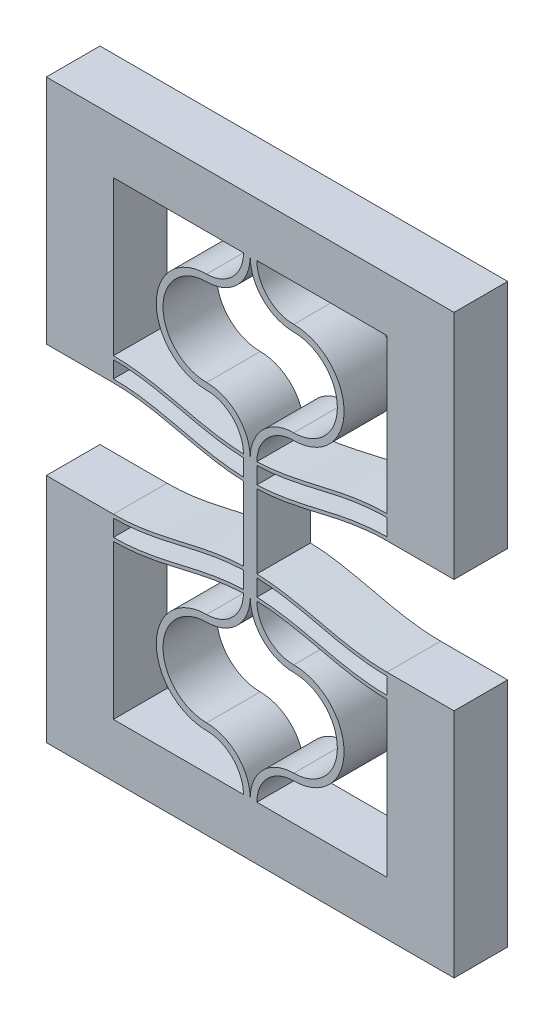
SolidWorks part; units mm, degrees
ref_plane "Front Plane" through (0, 0, 0) normal (0, 0, 1) x (1, 0, 0)
ref_plane "Top Plane" through (0, 0, 0) normal (0, 1, 0) x (1, 0, 0)
ref_plane "Right Plane" through (0, 0, 0) normal (1, 0, 0) x (0, 0, -1)
sketch "Sketch1" plane through (0, 0, 0) normal (0, 0, 1) x (1, 0, 0)
  line L4 (0, 11.5) -> (0, 0)
  line L5 (10.2, 0) -> (10.2, 13) construction
  line L6 (10.2, 13) -> (10.2, 15.9911) construction
  line L17 (9.7, 0) -> (0, 0)
  line L18 (10.7, 0) -> (20.4, 0)
  line L19 (20.4, 0) -> (20.4, 11.5)
  line L20 (10.7, 13.2411) -> (10.7, 14.4911)
  line L21 (9.7, 13.2411) -> (9.7, 14.4911)
  line L22 (10.7, 14.7411) -> (10.7, 15.9911)
  line L23 (10.7, 15.9911) -> (9.7, 15.9911)
  line L24 (9.7, 15.9911) -> (9.7, 14.7411)
  line L31 (-5, 13.25) -> (-5, -4)
  line L32 (-5, -4) -> (25.4, -4)
  line L33 (25.4, -4) -> (25.4, 13.25)
  line L34 (0, 11.75) -> (0, 13)
  line L36 (-5, 13.25) -> (0, 13.25)
  line L37 (25.4, 13.25) -> (20.4, 13.25)
  line L38 (20.4, 11.75) -> (20.4, 13)
  arc A0 (10.2, 13) -> (6.95, 9.75) centre (6.95, 13) cw
  arc A1 (6.95, 9.75) -> (6.95, 3.25) centre (6.95, 6.5) ccw
  arc A2 (6.95, 3.25) -> (10.2, 0) centre (6.95, 0) cw
  arc A3 (9.7, 12.9911) -> (6.95, 10.25) centre (6.95, 13) cw
  arc A4 (6.95, 10.25) -> (6.95, 2.75) centre (6.95, 6.5) ccw
  arc A5 (6.95, 2.75) -> (9.7, 0) centre (6.95, 0) cw
  arc A6 (9.7, 13) -> (6.95, 10.25) centre (6.95, 13) cw construction
  arc A7 (13.45, 3.25) -> (10.2, 0) centre (13.45, 0) ccw
  arc A8 (13.45, 2.75) -> (10.7, 0) centre (13.45, 0) ccw
  arc A9 (13.45, 9.75) -> (13.45, 3.25) centre (13.45, 6.5) cw
  arc A10 (13.45, 10.25) -> (13.45, 2.75) centre (13.45, 6.5) cw
  arc A11 (10.7, 12.9911) -> (13.45, 10.25) centre (13.45, 13) ccw
  arc A12 (10.2, 13) -> (13.45, 9.75) centre (13.45, 13) ccw
  spline S0 degree 4 poles (-2.0401, 11.8932) (-1.9772, 11.8846) (-1.8455, 11.8679) (-1.6624, 11.8447) (-1.3945, 11.8179) (-1.0936, 11.7897) (-0.7437, 11.7688) (-0.4752, 11.7554) (-0.0408, 11.749) (0.1102, 11.7499) (0.4738, 11.7558) (0.7092, 11.7679) (1.0334, 11.7851) (1.3516, 11.8128) (1.7502, 11.854) (2.1923, 11.9124) (2.7058, 11.9922) (3.3058, 12.1029) (4.0022, 12.2485) (4.9166, 12.4561) (5.9838, 12.707) (7.055, 12.9379) (8.1373, 13.1142) (9.0337, 13.2105) (9.8109, 13.2536) (10.5891, 13.2536) (11.3663, 13.2105) (12.2627, 13.1142) (13.3449, 12.9379) (14.4163, 12.707) (15.4832, 12.4561) (16.3198, 12.2662) (16.8578, 12.1523) (17.3629, 12.0533) (17.7764, 11.9798) (18.2035, 11.9124) (18.6563, 11.854) (18.9878, 11.8179) (19.2899, 11.793) (19.5137, 11.7765) (19.7423, 11.7659) (19.9174, 11.7558) (20.2941, 11.7499) (20.4363, 11.749) (20.8074, 11.7542) (21.0192, 11.7634) (21.2671, 11.7754) (21.4449, 11.7884) (21.6432, 11.8037) (21.8311, 11.8212) (22.0262, 11.8414) (22.2161, 11.864) (22.3445, 11.8804) (22.4082, 11.8889) (22.4399, 11.8932) knots 0 0 0 0 0 0.010394 0.020788 0.031182 0.041576 0.062112 0.07238 0.082649 0.098356 0.106209 0.114063 0.12977 0.145477 0.161184 0.176891 0.202819 0.228747 0.260161 0.291575 0.354403 0.405758 0.437172 0.468586 0.5 0.531414 0.562828 0.594242 0.645597 0.708425 0.739839 0.771253 0.784217 0.797181 0.823109 0.838816 0.854523 0.87023 0.878084 0.885937 0.893791 0.901644 0.917351 0.92762 0.937888 0.948156 0.958424 0.963621 0.968818 0.979212 0.989606 0.994803 1 1 1 1 1 construction
  spline S1 degree 4 poles (0, 11.75) (0.0812, 11.75) (0.1997, 11.7513) (0.4738, 11.7558) (0.7092, 11.7679) (1.0334, 11.7851) (1.3516, 11.8128) (1.7502, 11.854) (2.1923, 11.9124) (2.7058, 11.9922) (3.3058, 12.1029) (4.0022, 12.2485) (4.9166, 12.4561) (5.9838, 12.707) (7.055, 12.9379) (8.1373, 13.1142) (9.0337, 13.2105) (9.8109, 13.2536) (10.5891, 13.2536) (11.3663, 13.2105) (12.2627, 13.1142) (13.3449, 12.9379) (14.4163, 12.707) (15.4832, 12.4561) (16.3198, 12.2662) (16.8578, 12.1523) (17.3629, 12.0533) (17.7764, 11.9798) (18.2035, 11.9124) (18.6563, 11.854) (18.9878, 11.8179) (19.2899, 11.793) (19.5137, 11.7765) (19.7423, 11.7659) (19.9174, 11.7558) (20.2013, 11.7513) (20.3188, 11.75) (20.4, 11.75) knots 0.082649 0.082649 0.082649 0.082649 0.082649 0.098356 0.106209 0.114063 0.12977 0.145477 0.161184 0.176891 0.202819 0.228747 0.260161 0.291575 0.354403 0.405758 0.437172 0.468586 0.5 0.531414 0.562828 0.594242 0.645597 0.708425 0.739839 0.771253 0.784217 0.797181 0.823109 0.838816 0.854523 0.87023 0.878084 0.885937 0.893791 0.901644 0.917351 0.917351 0.917351 0.917351 0.917351
  spline S2 degree 4 poles (-2.0401, 13.1432) (-1.9772, 13.1346) (-1.8455, 13.1179) (-1.6624, 13.0947) (-1.3945, 13.0679) (-1.0936, 13.0397) (-0.7437, 13.0188) (-0.4752, 13.0054) (-0.0408, 12.999) (0.1102, 12.9999) (0.4738, 13.0058) (0.7092, 13.0179) (1.0334, 13.0351) (1.3516, 13.0628) (1.7502, 13.104) (2.1923, 13.1624) (2.7058, 13.2422) (3.3058, 13.3529) (4.0022, 13.4985) (4.9166, 13.7061) (5.9838, 13.957) (7.055, 14.1879) (8.1373, 14.3642) (9.0337, 14.4605) (9.8109, 14.5036) (10.5891, 14.5036) (11.3663, 14.4605) (12.2627, 14.3642) (13.3449, 14.1879) (14.4163, 13.957) (15.4832, 13.7061) (16.3198, 13.5162) (16.8578, 13.4023) (17.3629, 13.3033) (17.7764, 13.2298) (18.2035, 13.1624) (18.6563, 13.104) (18.9878, 13.0679) (19.2899, 13.043) (19.5137, 13.0265) (19.7423, 13.0159) (19.9174, 13.0058) (20.2941, 12.9999) (20.4363, 12.999) (20.8074, 13.0042) (21.0192, 13.0134) (21.2671, 13.0254) (21.4449, 13.0384) (21.6432, 13.0537) (21.8311, 13.0712) (22.0262, 13.0914) (22.2161, 13.114) (22.3445, 13.1304) (22.4082, 13.1389) (22.4399, 13.1432) knots 0 0 0 0 0 0.010394 0.020788 0.031182 0.041576 0.062112 0.07238 0.082649 0.098356 0.106209 0.114063 0.12977 0.145477 0.161184 0.176891 0.202819 0.228747 0.260161 0.291575 0.354403 0.405758 0.437172 0.468586 0.5 0.531414 0.562828 0.594242 0.645597 0.708425 0.739839 0.771253 0.784217 0.797181 0.823109 0.838816 0.854523 0.87023 0.878084 0.885937 0.893791 0.901644 0.917351 0.92762 0.937888 0.948156 0.958424 0.963621 0.968818 0.979212 0.989606 0.994803 1 1 1 1 1 construction
  spline S3 degree 4 poles (0, 13) (0.0812, 13) (0.1997, 13.0013) (0.4738, 13.0058) (0.7092, 13.0179) (1.0334, 13.0351) (1.3516, 13.0628) (1.7502, 13.104) (2.1923, 13.1624) (2.7058, 13.2422) (3.3058, 13.3529) (4.0022, 13.4985) (4.9166, 13.7061) (5.9838, 13.957) (7.055, 14.1879) (8.1373, 14.3642) (9.0337, 14.4605) (9.8109, 14.5036) (10.5891, 14.5036) (11.3663, 14.4605) (12.2627, 14.3642) (13.3449, 14.1879) (14.4163, 13.957) (15.4832, 13.7061) (16.3198, 13.5162) (16.8578, 13.4023) (17.3629, 13.3033) (17.7764, 13.2298) (18.2035, 13.1624) (18.6563, 13.104) (18.9878, 13.0679) (19.2899, 13.043) (19.5137, 13.0265) (19.7423, 13.0159) (19.9174, 13.0058) (20.2013, 13.0013) (20.3188, 13) (20.4, 13) knots 0.082649 0.082649 0.082649 0.082649 0.082649 0.098356 0.106209 0.114063 0.12977 0.145477 0.161184 0.176891 0.202819 0.228747 0.260161 0.291575 0.354403 0.405758 0.437172 0.468586 0.5 0.531414 0.562828 0.594242 0.645597 0.708425 0.739839 0.771253 0.784217 0.797181 0.823109 0.838816 0.854523 0.87023 0.878084 0.885937 0.893791 0.901644 0.917351 0.917351 0.917351 0.917351 0.917351
  spline S4 degree 4 poles (-2.0401, 13.3932) (-1.9772, 13.3846) (-1.8455, 13.3679) (-1.6624, 13.3447) (-1.3945, 13.3179) (-1.0936, 13.2897) (-0.7437, 13.2688) (-0.4752, 13.2554) (-0.0408, 13.249) (0.1102, 13.2499) (0.4738, 13.2558) (0.7092, 13.2679) (1.0334, 13.2851) (1.3516, 13.3128) (1.7502, 13.354) (2.1923, 13.4124) (2.7058, 13.4922) (3.3058, 13.6029) (4.0022, 13.7485) (4.9166, 13.9561) (5.9838, 14.207) (7.055, 14.4379) (8.1373, 14.6142) (9.0337, 14.7105) (9.8109, 14.7536) (10.5891, 14.7536) (11.3663, 14.7105) (12.2627, 14.6142) (13.3449, 14.4379) (14.4163, 14.207) (15.4832, 13.9561) (16.3198, 13.7662) (16.8578, 13.6523) (17.3629, 13.5533) (17.7764, 13.4798) (18.2035, 13.4124) (18.6563, 13.354) (18.9878, 13.3179) (19.2899, 13.293) (19.5137, 13.2765) (19.7423, 13.2659) (19.9174, 13.2558) (20.2941, 13.2499) (20.4363, 13.249) (20.8074, 13.2542) (21.0192, 13.2634) (21.2671, 13.2754) (21.4449, 13.2884) (21.6432, 13.3037) (21.8311, 13.3212) (22.0262, 13.3414) (22.2161, 13.364) (22.3445, 13.3804) (22.4082, 13.3889) (22.4399, 13.3932) knots 0 0 0 0 0 0.010394 0.020788 0.031182 0.041576 0.062112 0.07238 0.082649 0.098356 0.106209 0.114063 0.12977 0.145477 0.161184 0.176891 0.202819 0.228747 0.260161 0.291575 0.354403 0.405758 0.437172 0.468586 0.5 0.531414 0.562828 0.594242 0.645597 0.708425 0.739839 0.771253 0.784217 0.797181 0.823109 0.838816 0.854523 0.87023 0.878084 0.885937 0.893791 0.901644 0.917351 0.92762 0.937888 0.948156 0.958424 0.963621 0.968818 0.979212 0.989606 0.994803 1 1 1 1 1 construction
  spline S5 degree 4 poles (0, 13.25) (0.0812, 13.25) (0.1997, 13.2513) (0.4738, 13.2558) (0.7092, 13.2679) (1.0334, 13.2851) (1.3516, 13.3128) (1.7502, 13.354) (2.1923, 13.4124) (2.7058, 13.4922) (3.3058, 13.6029) (4.0022, 13.7485) (4.9166, 13.9561) (5.9838, 14.207) (7.055, 14.4379) (8.1373, 14.6142) (9.0337, 14.7105) (9.8109, 14.7536) (10.5891, 14.7536) (11.3663, 14.7105) (12.2627, 14.6142) (13.3449, 14.4379) (14.4163, 14.207) (15.4832, 13.9561) (16.3198, 13.7662) (16.8578, 13.6523) (17.3629, 13.5533) (17.7764, 13.4798) (18.2035, 13.4124) (18.6563, 13.354) (18.9878, 13.3179) (19.2899, 13.293) (19.5137, 13.2765) (19.7423, 13.2659) (19.9174, 13.2558) (20.2013, 13.2513) (20.3188, 13.25) (20.4, 13.25) knots 0.082649 0.082649 0.082649 0.082649 0.082649 0.098356 0.106209 0.114063 0.12977 0.145477 0.161184 0.176891 0.202819 0.228747 0.260161 0.291575 0.354403 0.405758 0.437172 0.468586 0.5 0.531414 0.562828 0.594242 0.645597 0.708425 0.739839 0.771253 0.784217 0.797181 0.823109 0.838816 0.854523 0.87023 0.878084 0.885937 0.893791 0.901644 0.917351 0.917351 0.917351 0.917351 0.917351
  spline S8 degree 4 poles (-2.0401, 11.6432) (-1.9772, 11.6346) (-1.8455, 11.6179) (-1.6624, 11.5947) (-1.3945, 11.5679) (-1.0936, 11.5397) (-0.7437, 11.5188) (-0.4752, 11.5054) (-0.0408, 11.499) (0.1102, 11.4999) (0.4738, 11.5058) (0.7092, 11.5179) (1.0334, 11.5351) (1.3516, 11.5628) (1.7502, 11.604) (2.1923, 11.6624) (2.7058, 11.7422) (3.3058, 11.8529) (4.0022, 11.9985) (4.9166, 12.2061) (5.9838, 12.457) (7.055, 12.6879) (8.1373, 12.8642) (9.0337, 12.9605) (9.8109, 13.0036) (10.5891, 13.0036) (11.3663, 12.9605) (12.2627, 12.8642) (13.3449, 12.6879) (14.4163, 12.457) (15.4832, 12.2061) (16.3198, 12.0162) (16.8578, 11.9023) (17.3629, 11.8033) (17.7764, 11.7298) (18.2035, 11.6624) (18.6563, 11.604) (18.9878, 11.5679) (19.2899, 11.543) (19.5137, 11.5265) (19.7423, 11.5159) (19.9174, 11.5058) (20.2941, 11.4999) (20.4363, 11.499) (20.8074, 11.5042) (21.0192, 11.5134) (21.2671, 11.5254) (21.4449, 11.5384) (21.6432, 11.5537) (21.8311, 11.5712) (22.0262, 11.5914) (22.2161, 11.614) (22.3445, 11.6304) (22.4082, 11.6389) (22.4399, 11.6432) knots 0 0 0 0 0 0.010394 0.020788 0.031182 0.041576 0.062112 0.07238 0.082649 0.098356 0.106209 0.114063 0.12977 0.145477 0.161184 0.176891 0.202819 0.228747 0.260161 0.291575 0.354403 0.405758 0.437172 0.468586 0.5 0.531414 0.562828 0.594242 0.645597 0.708425 0.739839 0.771253 0.784217 0.797181 0.823109 0.838816 0.854523 0.87023 0.878084 0.885937 0.893791 0.901644 0.917351 0.92762 0.937888 0.948156 0.958424 0.963621 0.968818 0.979212 0.989606 0.994803 1 1 1 1 1 construction
  spline S9 degree 4 poles (0, 11.5) (0.0812, 11.5) (0.1997, 11.5013) (0.4738, 11.5058) (0.7092, 11.5179) (1.0334, 11.5351) (1.3516, 11.5628) (1.7502, 11.604) (2.1923, 11.6624) (2.7058, 11.7422) (3.3058, 11.8529) (4.0022, 11.9985) (4.9166, 12.2061) (5.9838, 12.457) (7.055, 12.6879) (8.1373, 12.8642) (9.0337, 12.9605) (9.8109, 13.0036) (10.5891, 13.0036) (11.3663, 12.9605) (12.2627, 12.8642) (13.3449, 12.6879) (14.4163, 12.457) (15.4832, 12.2061) (16.3198, 12.0162) (16.8578, 11.9023) (17.3629, 11.8033) (17.7764, 11.7298) (18.2035, 11.6624) (18.6563, 11.604) (18.9878, 11.5679) (19.2899, 11.543) (19.5137, 11.5265) (19.7423, 11.5159) (19.9174, 11.5058) (20.2013, 11.5013) (20.3188, 11.5) (20.4, 11.5) knots 0.082649 0.082649 0.082649 0.082649 0.082649 0.098356 0.106209 0.114063 0.12977 0.145477 0.161184 0.176891 0.202819 0.228747 0.260161 0.291575 0.354403 0.405758 0.437172 0.468586 0.5 0.531414 0.562828 0.594242 0.645597 0.708425 0.739839 0.771253 0.784217 0.797181 0.823109 0.838816 0.854523 0.87023 0.878084 0.885937 0.893791 0.901644 0.917351 0.917351 0.917351 0.917351 0.917351
  dimension "D4" = 0.25
  dimension "D6" = 4
  dimension "D1" = 13
  dimension "D2" = 0.5
  dimension "D3" = 0.25
  dimension "D7" = 5
  dimension "D5" = 1.5
extrude "Boss-Extrude1" add sketch "Sketch1" along normal blind 4
sketch "Sketch4" plane through (0, 15.9911, 0) normal (0, 1, 0) x (1, 0, 0)
  line L24 (10.7, 0) -> (9.7, 0)
  line L25 (9.7, 0) -> (9.7, -4)
  line L26 (10.7, 0) -> (9.7, 0)
  line L27 (10.7, -4) -> (10.7, 0)
  line L29 (9.7, 0) -> (9.7, -4)
  line L31 (10.7, -4) -> (10.7, 0)
  line L32 (9.7, -4) -> (10.7, -4)
  line L33 (9.7, -4) -> (10.7, -4)
  dimension "D1" = 0
extrude "Boss-Extrude2" add sketch "Sketch4" along normal blind 1.5
mirror "Mirror3" about plane through (0, 17.4911, 0) normal (0, 1, 0) of bodies 179
ref_plane "Plane1" through (10.2, 0, 0) normal (-1, 0, 0) x (0, 0, 1)
split "Split2" [suppressed] bodies to split 247 102
sketch "Sketch7" [suppressed] plane through (10.2, 0, 0) normal (-1, 0, 0) x (0, 0, 1)
  line L4 (4, 34.9822) -> (4, 38.9822)
  line L12 (0, 13) -> (4, 13)
  line L13 (0, 13) -> (4, 13)
  line L14 (4, 13) -> (4, 21.9822)
  line L15 (4, 13) -> (4, 21.9822)
  line L20 (4, 0) -> (0, 0)
  line L22 (4, 0) -> (0, 0)
  line L23 (0, -4) -> (4, -4)
  line L27 (0, -4) -> (4, -4)
  line L31 (4, 21.9822) -> (0, 21.9822)
  line L32 (4, 21.9822) -> (0, 21.9822)
  line L33 (0, 21.9822) -> (0, 13)
  line L34 (0, 21.9822) -> (0, 13)
  line L36 (4, -4) -> (4, 0)
  line L38 (4, 34.9822) -> (4, 38.9822)
  line L39 (4, 34.9822) -> (4, 38.9822)
  line L40 (4, 38.9822) -> (0, 38.9822)
  line L41 (4, 38.9822) -> (0, 38.9822)
  line L46 (4, 34.9822) -> (4, 38.9822)
  line L51 (0, 38.9822) -> (0, 34.9822)
  line L52 (0, 38.9822) -> (0, 34.9822)
  line L53 (0, 34.9822) -> (4, 34.9822)
  line L54 (0, 34.9822) -> (4, 34.9822)
  line L55 (4, 38.9822) -> (0, 38.9822)
  line L57 (4, 38.9822) -> (0, 38.9822)
  line L59 (4, -4) -> (4, 0)
  line L60 (0, 0) -> (0, -4)
  line L61 (0, 0) -> (0, -4)
  line L62 (0, 38.9822) -> (0, 34.9822)
  line L63 (0, 38.9822) -> (0, 34.9822)
  line L64 (0, 34.9822) -> (4, 34.9822)
  line L65 (0, 34.9822) -> (4, 34.9822)
  dimension "D1" = 0
  dimension "D2" = 0
  dimension "D3" = 0
  dimension "D4" = 0
extrude "Boss-Extrude3" [suppressed] add sketch "Sketch7" along normal blind 4
mirror "Mirror2" [suppressed]
